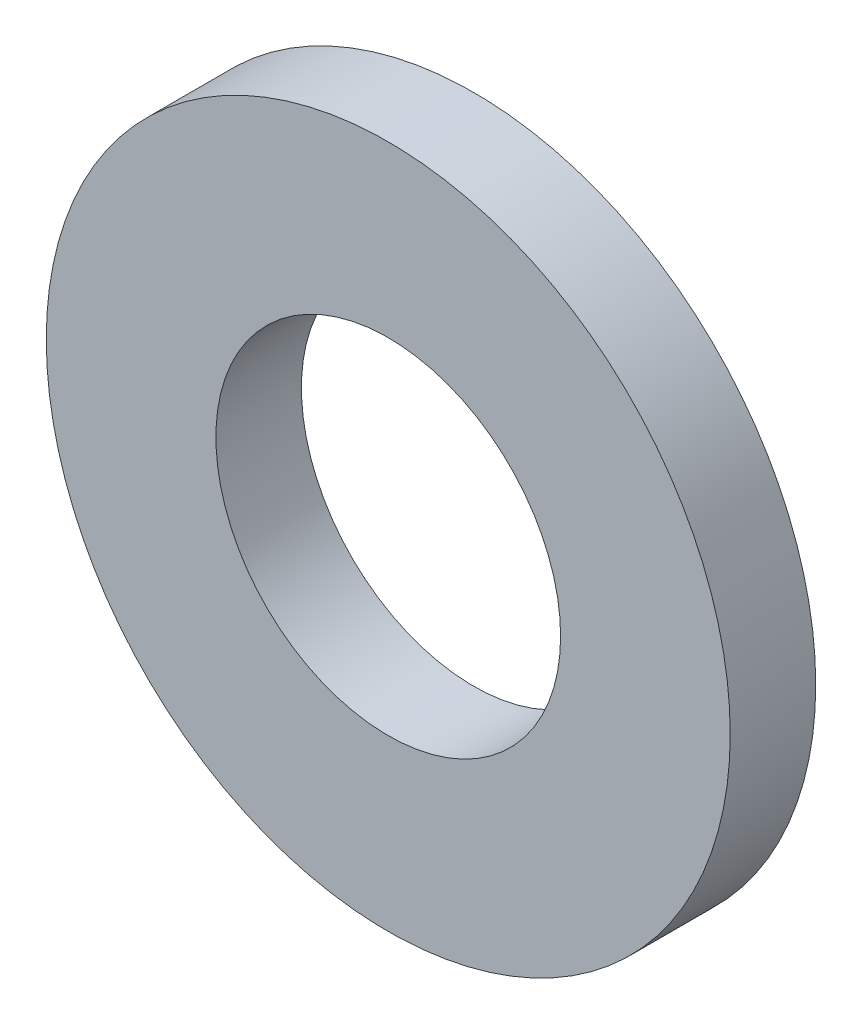
SolidWorks part; units mm, degrees
ref_plane "Front Plane" through (0, 0, 0) normal (0, 0, 1) x (1, 0, 0)
ref_plane "Top Plane" through (0, 0, 0) normal (0, 1, 0) x (1, 0, 0)
ref_plane "Right Plane" through (0, 0, 0) normal (1, 0, 0) x (0, 0, -1)
sketch "Sketch1" plane through (0, 0, 0) normal (0, 0, 1) x (1, 0, 0)
  circle A0 centre (0, 0) radius 6.4008
  circle A1 centre (0, 0) radius 12.7
  dimension "D1" = 25.4
  dimension "D2" = 12.8016
extrude "Boss-Extrude1" add sketch "Sketch1" along normal blind 3.175
